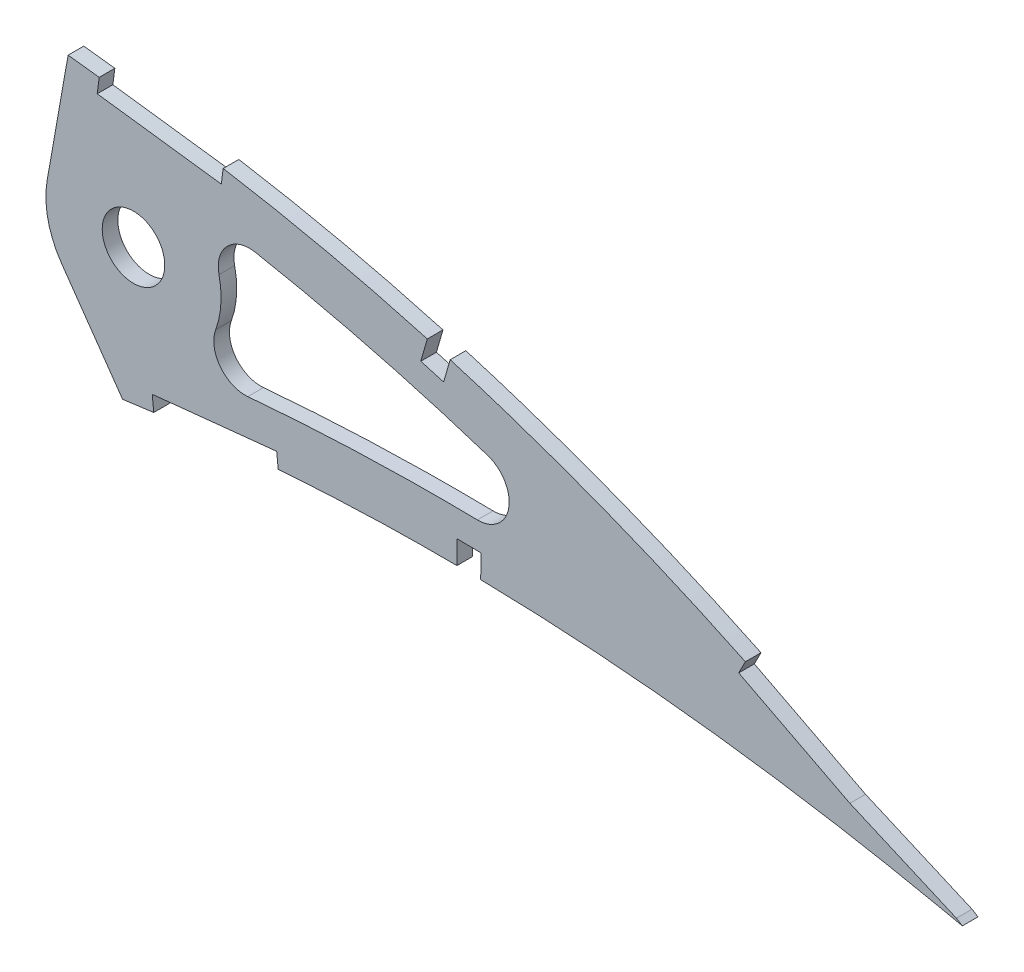
SolidWorks part; units mm, degrees
material "Plywood"
ref_plane "Front Plane" through (0, 0, 0) normal (0, 0, 1) x (1, 0, 0)
ref_plane "Top Plane" through (0, 0, 0) normal (0, 1, 0) x (1, 0, 0)
ref_plane "Right Plane" through (0, 0, 0) normal (1, 0, 0) x (0, 0, -1)
curve "Curve1"
  spline degree 3 poles (554.3197, 0.8642, 0) (554.2772, 0.8904, 0) (554.1075, 0.9953, 0) (553.7252, 1.2298, 0) (553.0885, 1.6204, 0) (552.1972, 2.1644, 0) (551.0519, 2.8603, 0) (549.6522, 3.7033, 0) (547.9988, 4.6906, 0) (546.0922, 5.8176, 0) (543.9326, 7.0789, 0) (541.5207, 8.4695, 0) (538.8569, 9.9815, 0) (535.942, 11.6087, 0) (532.7772, 13.3434, 0) (529.3631, 15.1777, 0) (525.7007, 17.1023, 0) (521.7917, 19.109, 0) (517.6366, 21.1866, 0) (513.2374, 23.3265, 0) (508.5956, 25.518, 0) (503.7128, 27.7495, 0) (498.5918, 30.0118, 0) (493.234, 32.2909, 0) (487.6424, 34.577, 0) (481.8195, 36.8569, 0) (475.7686, 39.1203, 0) (469.4922, 41.3526, 0) (462.9949, 43.5439, 0) (456.2798, 45.6802, 0) (449.3518, 47.7496, 0) (442.2149, 49.739, 0) (434.875, 51.6379, 0) (427.3368, 53.4327, 0) (419.6066, 55.1112, 0) (411.6907, 56.6635, 0) (403.5957, 58.0739, 0) (395.344, 59.3415, 0) (387.0683, 60.3958, 0) (378.8096, 61.4299, 0) (370.5633, 62.4014, 0) (362.2161, 63.3317, 0) (353.7762, 64.2156, 0) (345.252, 65.0503, 0) (336.6519, 65.8323, 0) (327.9851, 66.5592, 0) (319.2598, 67.227, 0) (310.4852, 67.8346, 0) (301.6702, 68.3766, 0) (292.8239, 68.8527, 0) (283.9555, 69.2595, 0) (275.0741, 69.5943, 0) (266.1892, 69.8549, 0) (257.3099, 70.039, 0) (248.446, 70.1454, 0) (239.6066, 70.171, 0) (230.8014, 70.1156, 0) (222.0395, 69.9772, 0) (213.3305, 69.7538, 0) (204.6838, 69.4452, 0) (196.1087, 69.0513, 0) (187.6145, 68.5689, 0) (179.2105, 68.0012, 0) (170.9059, 67.3456, 0) (162.7101, 66.6021, 0) (154.6315, 65.7736, 0) (146.6791, 64.8581, 0) (138.8614, 63.858, 0) (131.1871, 62.7754, 0) (123.6647, 61.6096, 0) (116.3022, 60.3641, 0) (109.1077, 59.04, 0) (102.0887, 57.6413, 0) (95.2529, 56.1683, 0) (88.6074, 54.6255, 0) (82.1593, 53.0155, 0) (75.9155, 51.3413, 0) (69.8822, 49.607, 0) (64.0656, 47.8163, 0) (58.4725, 45.9714, 0) (53.107, 44.0792, 0) (47.9758, 42.141, 0) (43.0829, 40.1629, 0) (38.4338, 38.1474, 0) (34.0322, 36.1008, 0) (29.883, 34.0255, 0) (25.9891, 31.9271, 0) (22.3545, 29.809, 0) (18.9827, 27.675, 0) (15.875, 25.5306, 0) (13.0358, 23.3771, 0) (10.4661, 21.22, 0) (8.1674, 19.0625, 0) (6.143, 16.9061, 0) (4.3929, 14.7547, 0) (2.9194, 12.6099, 0) (1.7228, 10.4738, 0) (0.8056, 8.3479, 0) (0.1671, 6.2334, 0) (-0.1824, 4.1334, 0) (-0.2694, 2.0463, 0) (-0.0897, 0.6811, 0) (0, 0, 0) knots 0 0 0 0 0.000254 0.001015 0.002283 0.004057 0.006331 0.009105 0.012374 0.016134 0.02038 0.025106 0.030306 0.035972 0.0421 0.048678 0.055702 0.06316 0.071046 0.07935 0.088063 0.097176 0.106678 0.116562 0.126814 0.137428 0.148394 0.1597 0.171338 0.183298 0.19557 0.208144 0.221012 0.234162 0.247587 0.261277 0.275223 0.289414 0.303771 0.317689 0.331784 0.34604 0.360444 0.374983 0.38964 0.404403 0.419257 0.434187 0.449177 0.464215 0.479284 0.49437 0.509458 0.524532 0.539579 0.554583 0.56953 0.584403 0.599191 0.613877 0.628447 0.642889 0.657186 0.671326 0.685294 0.699078 0.712665 0.726043 0.739198 0.752118 0.764792 0.777208 0.789356 0.801224 0.812804 0.824083 0.835055 0.84571 0.856038 0.866034 0.875689 0.884998 0.893953 0.902553 0.910789 0.918661 0.926166 0.933303 0.940071 0.946475 0.952518 0.958205 0.963547 0.968557 0.97325 0.977651 0.981787 0.985694 0.989415 0.993001 0.996508 1 1 1 1
curve "Curve2"
  spline degree 3 poles (0, 0, 0) (0.1423, -0.672, 0) (0.4277, -2.019, 0) (1.203, -3.9582, 0) (2.2282, -5.8223, 0) (3.5249, -7.6064, 0) (5.0845, -9.31, 0) (6.9036, -10.9348, 0) (8.9803, -12.4801, 0) (11.3119, -13.945, 0) (13.8951, -15.3312, 0) (16.7269, -16.6378, 0) (19.8048, -17.8643, 0) (23.1254, -19.0092, 0) (26.6846, -20.0741, 0) (30.4791, -21.0566, 0) (34.5045, -21.9578, 0) (38.7571, -22.7757, 0) (43.232, -23.5109, 0) (47.9248, -24.1631, 0) (52.8305, -24.7327, 0) (57.9444, -25.2185, 0) (63.2614, -25.6215, 0) (68.7762, -25.942, 0) (74.4834, -26.1811, 0) (80.3777, -26.3377, 0) (86.4531, -26.4144, 0) (92.7043, -26.4123, 0) (99.1251, -26.3308, 0) (105.71, -26.1745, 0) (112.4527, -25.9423, 0) (119.3471, -25.6371, 0) (126.387, -25.2619, 0) (133.5661, -24.818, 0) (140.8781, -24.3074, 0) (148.3166, -23.7341, 0) (155.8748, -23.0997, 0) (163.5462, -22.4077, 0) (171.324, -21.6617, 0) (179.2015, -20.864, 0) (187.1716, -20.0183, 0) (195.2274, -19.1275, 0) (203.3619, -18.1963, 0) (211.5677, -17.2262, 0) (219.8379, -16.223, 0) (228.1647, -15.1885, 0) (236.5412, -14.1266, 0) (244.9597, -13.0425, 0) (253.4125, -11.9359, 0) (261.8924, -10.8148, 0) (270.3912, -9.6781, 0) (278.9016, -8.5319, 0) (287.4156, -7.3796, 0) (295.925, -6.2216, 0) (304.4222, -5.0626, 0) (312.8995, -3.9059, 0) (321.3485, -2.7516, 0) (329.7616, -1.6054, 0) (338.1302, -0.4672, 0) (346.4467, 0.6607, 0) (354.7031, 1.775, 0) (362.8916, 2.8743, 0) (371.0037, 3.9578, 0) (379.0314, 5.0259, 0) (386.8463, 6.0463, 0) (394.4281, 7.0733, 0) (401.8022, 7.9152, 0) (409.0845, 8.6338, 0) (416.2825, 9.2229, 0) (423.3877, 9.6911, 0) (430.3918, 10.0417, 0) (437.2865, 10.2795, 0) (444.0631, 10.4116, 0) (450.7132, 10.4414, 0) (457.2276, 10.3785, 0) (463.598, 10.2277, 0) (469.8153, 9.9961, 0) (475.8709, 9.6912, 0) (481.7563, 9.3216, 0) (487.4626, 8.8925, 0) (492.9818, 8.4141, 0) (498.3055, 7.8933, 0) (503.4254, 7.336, 0) (508.334, 6.7541, 0) (513.0236, 6.1512, 0) (517.4871, 5.5374, 0) (521.7172, 4.9187, 0) (525.7074, 4.3032, 0) (529.4512, 3.6966, 0) (532.9427, 3.1071, 0) (536.1764, 2.5402, 0) (539.1467, 2.0013, 0) (541.8495, 1.4973, 0) (544.2794, 1.0307, 0) (546.4331, 0.6092, 0) (548.3068, 0.2346, 0) (549.8976, -0.0878, 0) (551.2027, -0.3567, 0) (552.2202, -0.5677, 0) (552.948, -0.7211, 0) (553.3854, -0.8124, 0) (553.5798, -0.8538, 0) (553.6283, -0.8642, 0) knots 0 0 0 0 0.003638 0.007293 0.011028 0.014901 0.018963 0.023258 0.027821 0.032679 0.037853 0.043362 0.049215 0.055422 0.061989 0.068918 0.076211 0.083868 0.091887 0.100266 0.109 0.118085 0.127515 0.137285 0.147388 0.157816 0.168563 0.179619 0.190977 0.202627 0.21456 0.226767 0.239236 0.251959 0.264924 0.27812 0.291536 0.30516 0.318981 0.332985 0.347163 0.361499 0.375981 0.390597 0.405333 0.420175 0.43511 0.450124 0.465203 0.480333 0.495501 0.51069 0.525887 0.541078 0.556247 0.571382 0.586466 0.601485 0.616424 0.631269 0.646007 0.660621 0.675098 0.689423 0.703582 0.716908 0.730009 0.742952 0.755726 0.76832 0.780724 0.792927 0.804916 0.816679 0.828204 0.839475 0.850481 0.861208 0.871639 0.881763 0.891564 0.901027 0.910139 0.918884 0.927249 0.935221 0.942785 0.949928 0.956638 0.962904 0.968712 0.974054 0.978918 0.983297 0.98718 0.990561 0.993433 0.995791 0.99763 0.998946 0.999737 1 1 1 1
sketch "Sketch1" plane through (0, 0, 0) normal (0, 0, 1) x (1, 0, 0)
  line L28 (0, 63.5) -> (-23.1981, 63.5) construction
  line L39 (379.9183, -27.3345) -> (379.9183, 27.3345) construction
  line L40 (368.4067, 59.4277) -> (353.2793, 2.9714) construction
  line L41 (537.5238, 0.838) -> (542.0214, -1.9404)
  line L42 (536.8534, -0.838) -> (542.0214, -1.9404)
  circle A0 centre (68.58, 6.35) radius 9.525 construction
  circle A1 centre (246.38, 6.35) radius 9.525 construction
  spline S3 degree 3 poles (0, 0) (0.138, -0.6516) (0.4147, -1.9578) (1.1665, -3.8383) (2.1607, -5.6459) (3.4181, -7.3759) (4.9305, -9.0279) (6.6944, -10.6035) (8.7082, -12.1019) (10.9692, -13.5225) (13.4741, -14.8667) (16.2201, -16.1336) (19.2047, -17.323) (22.4247, -18.4332) (25.8761, -19.4659) (29.5556, -20.4185) (33.4591, -21.2925) (37.5827, -22.0856) (41.9221, -22.7985) (46.4726, -23.431) (51.2297, -23.9833) (56.1887, -24.4544) (61.3446, -24.8452) (66.6923, -25.156) (72.2266, -25.3878) (77.9422, -25.5397) (83.8336, -25.6141) (89.8954, -25.612) (96.1216, -25.533) (102.507, -25.3814) (109.0454, -25.1563) (115.7309, -24.8603) (122.5575, -24.4965) (129.5191, -24.066) (136.6095, -23.5709) (143.8226, -23.015) (151.1518, -22.3997) (158.5908, -21.7287) (166.1329, -21.0053) (173.7717, -20.2318) (181.5003, -19.4118) (189.312, -18.5479) (197.2, -17.6449) (205.1572, -16.7043) (213.1768, -15.7315) (221.2513, -14.7283) (229.374, -13.6986) (237.5374, -12.6473) (245.7341, -11.5743) (253.957, -10.4871) (262.1983, -9.3849) (270.4508, -8.2734) (278.7069, -7.156) (286.9584, -6.033) (295.1983, -4.9092) (303.4187, -3.7876) (311.6117, -2.6683) (319.7698, -1.5568) (327.8848, -0.4531) (335.9493, 0.6407) (343.9556, 1.7212) (351.896, 2.7872) (359.7623, 3.8379) (367.5468, 4.8736) (375.1249, 5.8631) (382.4769, 6.859) (389.6276, 7.6754) (396.6892, 8.3722) (403.6691, 8.9435) (410.559, 9.3975) (417.3509, 9.7374) (424.0367, 9.968) (430.608, 10.0961) (437.0566, 10.1251) (443.3736, 10.064) (449.5509, 9.9178) (455.5799, 9.6932) (461.4521, 9.3976) (467.1591, 9.0391) (472.6925, 8.6231) (478.0445, 8.1591) (483.2068, 7.6541) (488.1716, 7.1138) (492.9315, 6.5494) (497.479, 5.9648) (501.8072, 5.3696) (505.9092, 4.7697) (509.7784, 4.1728) (513.4088, 3.5846) (516.7946, 3.013) (519.9303, 2.4632) (522.8106, 1.9407) (525.4315, 1.4519) (527.7877, 0.9995) (529.8762, 0.5907) (531.6931, 0.2275) (533.2357, -0.0851) (534.5012, -0.3459) (535.4879, -0.5505) (536.1937, -0.6992) (536.6178, -0.7878) (536.8063, -0.828) (536.8534, -0.838) knots 0 0 0 0 0.003638 0.007293 0.011028 0.014901 0.018963 0.023258 0.027821 0.032679 0.037853 0.043362 0.049215 0.055422 0.061989 0.068918 0.076211 0.083868 0.091887 0.100266 0.109 0.118085 0.127515 0.137285 0.147388 0.157816 0.168563 0.179619 0.190977 0.202627 0.21456 0.226767 0.239236 0.251959 0.264924 0.27812 0.291536 0.30516 0.318981 0.332985 0.347163 0.361499 0.375981 0.390597 0.405333 0.420175 0.43511 0.450124 0.465203 0.480333 0.495501 0.51069 0.525887 0.541078 0.556247 0.571382 0.586466 0.601485 0.616424 0.631269 0.646007 0.660621 0.675098 0.689423 0.703582 0.716908 0.730009 0.742952 0.755726 0.76832 0.780724 0.792927 0.804916 0.816679 0.828204 0.839475 0.850481 0.861208 0.871639 0.881763 0.891564 0.901027 0.910139 0.918884 0.927249 0.935221 0.942785 0.949928 0.956638 0.962904 0.968712 0.974054 0.978918 0.983297 0.98718 0.990561 0.993433 0.995791 0.99763 0.998946 0.999737 1 1 1 1
  spline S6 degree 3 poles (537.5238, 0.838) (537.4826, 0.8635) (537.3181, 0.9651) (536.9473, 1.1925) (536.3299, 1.5713) (535.4656, 2.0988) (534.3551, 2.7737) (532.9977, 3.5911) (531.3944, 4.5485) (529.5456, 5.6413) (527.4514, 6.8644) (525.1126, 8.2129) (522.5295, 9.6791) (519.703, 11.2569) (516.6341, 12.9391) (513.3234, 14.7178) (509.772, 16.5841) (505.9814, 18.53) (501.9522, 20.5446) (497.6863, 22.6197) (493.1852, 24.7448) (488.4503, 26.9087) (483.4845, 29.1025) (478.289, 31.3125) (472.8669, 33.5293) (467.2204, 35.7401) (461.3528, 37.9349) (455.2666, 40.0996) (448.9661, 42.2246) (442.4545, 44.296) (435.7364, 46.3028) (428.8157, 48.2319) (421.6983, 50.0733) (414.3885, 51.8137) (406.8926, 53.4414) (399.2165, 54.9466) (391.3668, 56.3143) (383.365, 57.5434) (375.3401, 58.5658) (367.3317, 59.5686) (359.3352, 60.5106) (351.241, 61.4127) (343.0568, 62.2698) (334.7908, 63.0793) (326.4514, 63.8376) (318.0471, 64.5425) (309.5862, 65.19) (301.0775, 65.7792) (292.5296, 66.3048) (283.9513, 66.7665) (275.3516, 67.161) (266.7393, 67.4856) (258.1236, 67.7383) (249.5134, 67.9168) (240.9181, 68.0199) (232.3465, 68.0449) (223.8081, 67.9911) (215.3117, 67.8569) (206.8666, 67.6403) (198.4819, 67.341) (190.1666, 66.959) (181.9298, 66.4913) (173.7804, 65.9407) (165.7275, 65.305) (157.78, 64.584) (149.9461, 63.7807) (142.2347, 62.8929) (134.6539, 61.9231) (127.2121, 60.8733) (119.9176, 59.7429) (112.7783, 58.535) (105.8017, 57.2511) (98.9954, 55.8947) (92.3667, 54.4664) (85.9226, 52.9703) (79.6699, 51.4091) (73.6153, 49.7857) (67.7648, 48.1039) (62.1244, 46.3675) (56.7008, 44.5785) (51.4979, 42.7436) (46.5222, 40.8641) (41.7775, 38.9459) (37.2693, 36.9916) (33.0011, 35.007) (28.9776, 32.9945) (25.2017, 30.9597) (21.6772, 28.9058) (18.4075, 26.8364) (15.394, 24.757) (12.6408, 22.6688) (10.1489, 20.577) (7.9199, 18.4849) (5.9569, 16.3939) (4.2598, 14.3076) (2.831, 12.2278) (1.6706, 10.1565) (0.7812, 8.095) (0.162, 6.0445) (-0.1769, 4.0082) (-0.2612, 1.9843) (-0.087, 0.6604) (0, 0) knots 0 0 0 0 0.000254 0.001015 0.002283 0.004057 0.006331 0.009105 0.012374 0.016134 0.02038 0.025106 0.030306 0.035972 0.0421 0.048678 0.055702 0.06316 0.071046 0.07935 0.088063 0.097176 0.106678 0.116562 0.126814 0.137428 0.148394 0.1597 0.171338 0.183298 0.19557 0.208144 0.221012 0.234162 0.247587 0.261277 0.275223 0.289414 0.303771 0.317689 0.331784 0.34604 0.360444 0.374983 0.38964 0.404403 0.419257 0.434187 0.449177 0.464215 0.479284 0.49437 0.509458 0.524532 0.539579 0.554583 0.56953 0.584403 0.599191 0.613877 0.628447 0.642889 0.657186 0.671326 0.685294 0.699078 0.712665 0.726043 0.739198 0.752118 0.764792 0.777208 0.789356 0.801224 0.812804 0.824083 0.835055 0.84571 0.856038 0.866034 0.875689 0.884998 0.893953 0.902553 0.910789 0.918661 0.926166 0.933303 0.940071 0.946475 0.952518 0.958205 0.963547 0.968557 0.97325 0.977651 0.981787 0.985694 0.989415 0.993001 0.996508 1 1 1 1
  point P10 (78.5929, 16.5948)
  point P11 (227.8303, 32.4941)
  dimension "D2" = 19.05
  dimension "D18" = 177.8
  dimension "D3" = 15
  dimension "D5" = 63.5
  dimension "D7" = 57.15
  dimension "D12" = 57.15
  dimension "D17" = 68.58
extrude "Boss-Extrude1" add sketch "Sketch1" along normal blind 3.175
sketch "Sketch4" plane through (0, 0, 0) normal (0, 0, -1) x (-1, 0, 0)
  line L0 (-356.287, 36.32) -> (-360.5267, 60.365)
  line L1 (-359.2323, 23.0344) -> (-371.5795, 5.4008)
  line L2 (-373.7968, 33.2326) -> (-412.6852, 33.2326)
  circle A0 centre (-373.7968, 33.2326) radius 17.78
  circle A1 centre (-373.7968, 33.2326) radius 6.35
  spline S0 degree 3 poles (-1632.0302, 1674.0962) (-565.4284, -22.6918) (-552.7247, -8.4851) (-536.9473, 1.1925) (-536.3299, 1.5713) (-535.4656, 2.0988) (-534.3551, 2.7737) (-532.9977, 3.5911) (-531.3944, 4.5485) (-529.5456, 5.6413) (-527.4514, 6.8644) (-525.1126, 8.2129) (-522.5295, 9.6791) (-519.703, 11.2569) (-516.6341, 12.9391) (-513.3234, 14.7178) (-509.772, 16.5841) (-505.9814, 18.53) (-501.9522, 20.5446) (-497.6863, 22.6197) (-493.1852, 24.7448) (-488.4503, 26.9087) (-483.4845, 29.1025) (-478.289, 31.3125) (-472.8669, 33.5293) (-467.2204, 35.7401) (-461.3528, 37.9349) (-455.2666, 40.0996) (-448.9661, 42.2246) (-442.4545, 44.296) (-435.7364, 46.3028) (-428.8157, 48.2319) (-421.6983, 50.0733) (-414.3885, 51.8137) (-406.8926, 53.4414) (-399.2165, 54.9466) (-391.3668, 56.3143) (-383.365, 57.5434) (-375.3401, 58.5658) (-367.3317, 59.5686) (-359.3352, 60.5106) (-351.241, 61.4127) (-343.0568, 62.2698) (-334.7908, 63.0793) (-326.4514, 63.8376) (-318.0471, 64.5425) (-309.5862, 65.19) (-301.0775, 65.7792) (-292.5296, 66.3048) (-283.9513, 66.7665) (-275.3516, 67.161) (-266.7393, 67.4856) (-258.1236, 67.7383) (-249.5134, 67.9168) (-240.9181, 68.0199) (-232.3465, 68.0449) (-223.8081, 67.9911) (-215.3117, 67.8569) (-206.8666, 67.6403) (-198.4819, 67.341) (-190.1666, 66.959) (-181.9298, 66.4913) (-173.7804, 65.9407) (-165.7275, 65.305) (-157.78, 64.584) (-149.9461, 63.7807) (-142.2347, 62.8929) (-134.6539, 61.9231) (-127.2121, 60.8733) (-119.9176, 59.7429) (-112.7783, 58.535) (-105.8017, 57.2511) (-98.9954, 55.8947) (-92.3667, 54.4664) (-85.9226, 52.9703) (-79.6699, 51.4091) (-73.6153, 49.7857) (-67.7648, 48.1039) (-62.1244, 46.3675) (-56.7008, 44.5785) (-51.4979, 42.7436) (-46.5222, 40.8641) (-41.7775, 38.9459) (-37.2693, 36.9916) (-33.0011, 35.007) (-28.9776, 32.9945) (-25.2017, 30.9597) (-21.6772, 28.9058) (-18.4075, 26.8364) (-15.394, 24.757) (-12.6408, 22.6688) (-10.1489, 20.577) (-7.9199, 18.4849) (-5.9569, 16.3939) (-4.2598, 14.3076) (-2.831, 12.2278) (-1.6706, 10.1565) (-0.7812, 8.095) (-0.162, 6.0445) (0.1769, 4.0082) (1.1707, -19.8347) (-66.7598, -38.6935) (1990.434, -189.4699) knots -0.094882 -0.094882 -0.094882 -0.094882 0.000254 0.001015 0.002283 0.004057 0.006331 0.009105 0.012374 0.016134 0.02038 0.025106 0.030306 0.035972 0.0421 0.048678 0.055702 0.06316 0.071046 0.07935 0.088063 0.097176 0.106678 0.116562 0.126814 0.137428 0.148394 0.1597 0.171338 0.183298 0.19557 0.208144 0.221012 0.234162 0.247587 0.261277 0.275223 0.289414 0.303771 0.317689 0.331784 0.34604 0.360444 0.374983 0.38964 0.404403 0.419257 0.434187 0.449177 0.464215 0.479284 0.49437 0.509458 0.524532 0.539579 0.554583 0.56953 0.584403 0.599191 0.613877 0.628447 0.642889 0.657186 0.671326 0.685294 0.699078 0.712665 0.726043 0.739198 0.752118 0.764792 0.777208 0.789356 0.801224 0.812804 0.824083 0.835055 0.84571 0.856038 0.866034 0.875689 0.884998 0.893953 0.902553 0.910789 0.918661 0.926166 0.933303 0.940071 0.946475 0.952518 0.958205 0.963547 0.968557 0.97325 0.977651 0.981787 0.985694 0.989415 0.993001 0.996508 1.114113 1.114113 1.114113 1.114113 only from (-537.5238, 0.838) to (0, 0) construction
  spline S1 degree 3 poles (1940.1203, -483.4322) (-49.9299, 58.7424) (7.7069, 18.357) (-1.1665, -3.8383) (-2.1607, -5.6459) (-3.4181, -7.3759) (-4.9305, -9.0279) (-6.6944, -10.6035) (-8.7082, -12.1019) (-10.9692, -13.5225) (-13.4741, -14.8667) (-16.2201, -16.1336) (-19.2047, -17.323) (-22.4247, -18.4332) (-25.8761, -19.4659) (-29.5556, -20.4185) (-33.4591, -21.2925) (-37.5827, -22.0856) (-41.9221, -22.7985) (-46.4726, -23.431) (-51.2297, -23.9833) (-56.1887, -24.4544) (-61.3446, -24.8452) (-66.6923, -25.156) (-72.2266, -25.3878) (-77.9422, -25.5397) (-83.8336, -25.6141) (-89.8954, -25.612) (-96.1216, -25.533) (-102.507, -25.3814) (-109.0454, -25.1563) (-115.7309, -24.8603) (-122.5575, -24.4965) (-129.5191, -24.066) (-136.6095, -23.5709) (-143.8226, -23.015) (-151.1518, -22.3997) (-158.5908, -21.7287) (-166.1329, -21.0053) (-173.7717, -20.2318) (-181.5003, -19.4118) (-189.312, -18.5479) (-197.2, -17.6449) (-205.1572, -16.7043) (-213.1768, -15.7315) (-221.2513, -14.7283) (-229.374, -13.6986) (-237.5374, -12.6473) (-245.7341, -11.5743) (-253.957, -10.4871) (-262.1983, -9.3849) (-270.4508, -8.2734) (-278.7069, -7.156) (-286.9584, -6.033) (-295.1983, -4.9092) (-303.4187, -3.7876) (-311.6117, -2.6683) (-319.7698, -1.5568) (-327.8848, -0.4531) (-335.9493, 0.6407) (-343.9556, 1.7212) (-351.896, 2.7872) (-359.7623, 3.8379) (-367.5468, 4.8736) (-375.1249, 5.8631) (-382.4769, 6.859) (-389.6276, 7.6754) (-396.6892, 8.3722) (-403.6691, 8.9435) (-410.559, 9.3975) (-417.3509, 9.7374) (-424.0367, 9.968) (-430.608, 10.0961) (-437.0566, 10.1251) (-443.3736, 10.064) (-449.5509, 9.9178) (-455.5799, 9.6932) (-461.4521, 9.3976) (-467.1591, 9.0391) (-472.6925, 8.6231) (-478.0445, 8.1591) (-483.2068, 7.6541) (-488.1716, 7.1138) (-492.9315, 6.5494) (-497.479, 5.9648) (-501.8072, 5.3696) (-505.9092, 4.7697) (-509.7784, 4.1728) (-513.4088, 3.5846) (-516.7946, 3.013) (-519.9303, 2.4632) (-522.8106, 1.9407) (-525.4315, 1.4519) (-527.7877, 0.9995) (-529.8762, 0.5907) (-531.6931, 0.2275) (-533.2357, -0.0851) (-534.5012, -0.3459) (-535.4879, -0.5505) (-536.1937, -0.6992) (-552.4366, -4.0895) (-567.1821, -13.3973) (-997.8539, 1944.6618) knots -0.119141 -0.119141 -0.119141 -0.119141 0.003638 0.007293 0.011028 0.014901 0.018963 0.023258 0.027821 0.032679 0.037853 0.043362 0.049215 0.055422 0.061989 0.068918 0.076211 0.083868 0.091887 0.100266 0.109 0.118085 0.127515 0.137285 0.147388 0.157816 0.168563 0.179619 0.190977 0.202627 0.21456 0.226767 0.239236 0.251959 0.264924 0.27812 0.291536 0.30516 0.318981 0.332985 0.347163 0.361499 0.375981 0.390597 0.405333 0.420175 0.43511 0.450124 0.465203 0.480333 0.495501 0.51069 0.525887 0.541078 0.556247 0.571382 0.586466 0.601485 0.616424 0.631269 0.646007 0.660621 0.675098 0.689423 0.703582 0.716908 0.730009 0.742952 0.755726 0.76832 0.780724 0.792927 0.804916 0.816679 0.828204 0.839475 0.850481 0.861208 0.871639 0.881763 0.891564 0.901027 0.910139 0.918884 0.927249 0.935221 0.942785 0.949928 0.956638 0.962904 0.968712 0.974054 0.978918 0.983297 0.98718 0.990561 0.993433 0.995791 0.99763 0.998946 0.999737 1.088404 1.088404 1.088404 1.088404 only from (0, 0) to (-536.8534, -0.838) construction
  spline S2 degree 3 poles (-537.5238, 0.838) (-537.4826, 0.8635) (-537.3181, 0.9651) (-536.9473, 1.1925) (-536.3299, 1.5713) (-535.4656, 2.0988) (-534.3551, 2.7737) (-532.9977, 3.5911) (-531.3944, 4.5485) (-529.5456, 5.6413) (-527.4514, 6.8644) (-525.1126, 8.2129) (-522.5295, 9.6791) (-519.703, 11.2569) (-516.6341, 12.9391) (-513.3234, 14.7178) (-509.772, 16.5841) (-505.9814, 18.53) (-501.9522, 20.5446) (-497.6863, 22.6197) (-493.1852, 24.7448) (-488.4503, 26.9087) (-483.4845, 29.1025) (-478.289, 31.3125) (-472.8669, 33.5293) (-467.2204, 35.7401) (-461.3528, 37.9349) (-455.2666, 40.0996) (-448.9661, 42.2246) (-442.4545, 44.296) (-435.7364, 46.3028) (-428.8157, 48.2319) (-421.6983, 50.0733) (-414.3885, 51.8137) (-406.8926, 53.4414) (-399.2165, 54.9466) (-391.3668, 56.3143) (-383.365, 57.5434) (-375.3401, 58.5658) (-367.3317, 59.5686) (-359.3352, 60.5106) (-351.241, 61.4127) (-343.0568, 62.2698) (-334.7908, 63.0793) (-326.4514, 63.8376) (-318.0471, 64.5425) (-309.5862, 65.19) (-301.0775, 65.7792) (-292.5296, 66.3048) (-283.9513, 66.7665) (-275.3516, 67.161) (-266.7393, 67.4856) (-258.1236, 67.7383) (-249.5134, 67.9168) (-240.9181, 68.0199) (-232.3465, 68.0449) (-223.8081, 67.9911) (-215.3117, 67.8569) (-206.8666, 67.6403) (-198.4819, 67.341) (-190.1666, 66.959) (-181.9298, 66.4913) (-173.7804, 65.9407) (-165.7275, 65.305) (-157.78, 64.584) (-149.9461, 63.7807) (-142.2347, 62.8929) (-134.6539, 61.9231) (-127.2121, 60.8733) (-119.9176, 59.7429) (-112.7783, 58.535) (-105.8017, 57.2511) (-98.9954, 55.8947) (-92.3667, 54.4664) (-85.9226, 52.9703) (-79.6699, 51.4091) (-73.6153, 49.7857) (-67.7648, 48.1039) (-62.1244, 46.3675) (-56.7008, 44.5785) (-51.4979, 42.7436) (-46.5222, 40.8641) (-41.7775, 38.9459) (-37.2693, 36.9916) (-33.0011, 35.007) (-28.9776, 32.9945) (-25.2017, 30.9597) (-21.6772, 28.9058) (-18.4075, 26.8364) (-15.394, 24.757) (-12.6408, 22.6688) (-10.1489, 20.577) (-7.9199, 18.4849) (-5.9569, 16.3939) (-4.2598, 14.3076) (-2.831, 12.2278) (-1.6706, 10.1565) (-0.7812, 8.095) (-0.162, 6.0445) (0.1769, 4.0082) (0.2612, 1.9843) (0.087, 0.6604) (0, 0) knots 0 0 0 0 0.000254 0.001015 0.002283 0.004057 0.006331 0.009105 0.012374 0.016134 0.02038 0.025106 0.030306 0.035972 0.0421 0.048678 0.055702 0.06316 0.071046 0.07935 0.088063 0.097176 0.106678 0.116562 0.126814 0.137428 0.148394 0.1597 0.171338 0.183298 0.19557 0.208144 0.221012 0.234162 0.247587 0.261277 0.275223 0.289414 0.303771 0.317689 0.331784 0.34604 0.360444 0.374983 0.38964 0.404403 0.419257 0.434187 0.449177 0.464215 0.479284 0.49437 0.509458 0.524532 0.539579 0.554583 0.56953 0.584403 0.599191 0.613877 0.628447 0.642889 0.657186 0.671326 0.685294 0.699078 0.712665 0.726043 0.739198 0.752118 0.764792 0.777208 0.789356 0.801224 0.812804 0.824083 0.835055 0.84571 0.856038 0.866034 0.875689 0.884998 0.893953 0.902553 0.910789 0.918661 0.926166 0.933303 0.940071 0.946475 0.952518 0.958205 0.963547 0.968557 0.97325 0.977651 0.981787 0.985694 0.989415 0.993001 0.996508 1 1 1 1
  spline S3 degree 3 poles (0, 0) (-0.138, -0.6516) (-0.4147, -1.9578) (-1.1665, -3.8383) (-2.1607, -5.6459) (-3.4181, -7.3759) (-4.9305, -9.0279) (-6.6944, -10.6035) (-8.7082, -12.1019) (-10.9692, -13.5225) (-13.4741, -14.8667) (-16.2201, -16.1336) (-19.2047, -17.323) (-22.4247, -18.4332) (-25.8761, -19.4659) (-29.5556, -20.4185) (-33.4591, -21.2925) (-37.5827, -22.0856) (-41.9221, -22.7985) (-46.4726, -23.431) (-51.2297, -23.9833) (-56.1887, -24.4544) (-61.3446, -24.8452) (-66.6923, -25.156) (-72.2266, -25.3878) (-77.9422, -25.5397) (-83.8336, -25.6141) (-89.8954, -25.612) (-96.1216, -25.533) (-102.507, -25.3814) (-109.0454, -25.1563) (-115.7309, -24.8603) (-122.5575, -24.4965) (-129.5191, -24.066) (-136.6095, -23.5709) (-143.8226, -23.015) (-151.1518, -22.3997) (-158.5908, -21.7287) (-166.1329, -21.0053) (-173.7717, -20.2318) (-181.5003, -19.4118) (-189.312, -18.5479) (-197.2, -17.6449) (-205.1572, -16.7043) (-213.1768, -15.7315) (-221.2513, -14.7283) (-229.374, -13.6986) (-237.5374, -12.6473) (-245.7341, -11.5743) (-253.957, -10.4871) (-262.1983, -9.3849) (-270.4508, -8.2734) (-278.7069, -7.156) (-286.9584, -6.033) (-295.1983, -4.9092) (-303.4187, -3.7876) (-311.6117, -2.6683) (-319.7698, -1.5568) (-327.8848, -0.4531) (-335.9493, 0.6407) (-343.9556, 1.7212) (-351.896, 2.7872) (-359.7623, 3.8379) (-367.5468, 4.8736) (-375.1249, 5.8631) (-382.4769, 6.859) (-389.6276, 7.6754) (-396.6892, 8.3722) (-403.6691, 8.9435) (-410.559, 9.3975) (-417.3509, 9.7374) (-424.0367, 9.968) (-430.608, 10.0961) (-437.0566, 10.1251) (-443.3736, 10.064) (-449.5509, 9.9178) (-455.5799, 9.6932) (-461.4521, 9.3976) (-467.1591, 9.0391) (-472.6925, 8.6231) (-478.0445, 8.1591) (-483.2068, 7.6541) (-488.1716, 7.1138) (-492.9315, 6.5494) (-497.479, 5.9648) (-501.8072, 5.3696) (-505.9092, 4.7697) (-509.7784, 4.1728) (-513.4088, 3.5846) (-516.7946, 3.013) (-519.9303, 2.4632) (-522.8106, 1.9407) (-525.4315, 1.4519) (-527.7877, 0.9995) (-529.8762, 0.5907) (-531.6931, 0.2275) (-533.2357, -0.0851) (-534.5012, -0.3459) (-535.4879, -0.5505) (-536.1937, -0.6992) (-536.6178, -0.7878) (-536.8063, -0.828) (-536.8534, -0.838) knots 0 0 0 0 0.003638 0.007293 0.011028 0.014901 0.018963 0.023258 0.027821 0.032679 0.037853 0.043362 0.049215 0.055422 0.061989 0.068918 0.076211 0.083868 0.091887 0.100266 0.109 0.118085 0.127515 0.137285 0.147388 0.157816 0.168563 0.179619 0.190977 0.202627 0.21456 0.226767 0.239236 0.251959 0.264924 0.27812 0.291536 0.30516 0.318981 0.332985 0.347163 0.361499 0.375981 0.390597 0.405333 0.420175 0.43511 0.450124 0.465203 0.480333 0.495501 0.51069 0.525887 0.541078 0.556247 0.571382 0.586466 0.601485 0.616424 0.631269 0.646007 0.660621 0.675098 0.689423 0.703582 0.716908 0.730009 0.742952 0.755726 0.76832 0.780724 0.792927 0.804916 0.816679 0.828204 0.839475 0.850481 0.861208 0.871639 0.881763 0.891564 0.901027 0.910139 0.918884 0.927249 0.935221 0.942785 0.949928 0.956638 0.962904 0.968712 0.974054 0.978918 0.983297 0.98718 0.990561 0.993433 0.995791 0.99763 0.998946 0.999737 1 1 1 1
  spline S4 degree 1 poles (-532.1841, -7.8057) (-10.0219, 1.7185) knots 0 0 1 1 construction
  spline S5 degree 1 poles (-10.0219, 1.7185) (-538.9729, 9.0984) knots 0 0 1 1 construction
  spline S6 degree 3 poles (-532.1841, -7.8057) (-532.035, -7.7136) (-531.7436, -7.5345) (-531.1023, -7.1412) (-530.0303, -6.4862) (-527.85, -5.1645) (-523.4829, -2.5651) (-514.6678, 2.5066) (-496.7411, 12.095) (-470.3238, 24.1396) (-442.9694, 33.791) (-420.6386, 39.9785) (-406.5149, 43.1961) (-395.1531, 45.3637) (-386.5599, 46.8051) (-378.0384, 47.9972) (-369.1749, 49.1011) (-360.4166, 50.162) (-348.6799, 51.484) (-328.147, 53.5808) (-298.749, 55.9238) (-263.4315, 57.6196) (-228.1119, 58.0844) (-192.8506, 57.171) (-157.7356, 54.6709) (-128.7085, 51.0365) (-105.7459, 46.987) (-88.7097, 43.306) (-71.9299, 38.8842) (-58.261, 34.4734) (-47.6305, 30.4115) (-39.8596, 27.063) (-32.3674, 23.3733) (-25.2794, 19.2928) (-18.8179, 14.7781) (-14.319, 10.6534) (-11.7187, 7.3378) (-10.6606, 5.4268) (-10.2382, 4.2645) (-10.0884, 3.6968) (-10.0101, 3.295) (-9.9553, 2.8496) (-9.9432, 2.5723) (-9.9453, 2.4518) (-9.9493, 2.3713) (-9.9688, 2.1598) (-9.9949, 1.9339) (-10.0132, 1.7875) (-10.0219, 1.7185) knots 0 0 0 0 0.000976 0.001952 0.003903 0.007807 0.015613 0.031226 0.062452 0.124904 0.187357 0.218583 0.249809 0.265422 0.281035 0.296648 0.312261 0.327874 0.343487 0.374713 0.437166 0.499618 0.56207 0.624522 0.686974 0.749427 0.780653 0.811879 0.843105 0.874331 0.889944 0.905557 0.92117 0.936783 0.952396 0.968009 0.975816 0.983623 0.987526 0.989477 0.991429 0.993381 0.995332 0.996308 0.997284 0.99826 0.998748 0.999236 0.999236 0.999236 0.999236
  spline S7 degree 3 poles (-10.0219, 1.7185) (-10.0361, 1.6529) (-10.0665, 1.5144) (-10.1157, 1.2979) (-10.1669, 1.0931) (-10.1938, 1.0009) (-10.2267, 0.9008) (-10.3197, 0.6625) (-10.5705, 0.1458) (-10.9157, -0.4199) (-11.7404, -1.469) (-13.2635, -2.8937) (-16.5705, -5.1355) (-21.8641, -7.6046) (-29.0738, -9.8943) (-36.7462, -11.652) (-44.6834, -12.9788) (-52.7844, -13.9626) (-63.7273, -14.8945) (-77.583, -15.4719) (-94.3476, -15.4772) (-111.1866, -14.9569) (-133.6938, -13.7131) (-161.8825, -11.3422) (-195.7357, -7.6685) (-229.6092, -3.472) (-263.4966, 1.0208) (-297.4142, 5.6457) (-325.6956, 9.51) (-345.5133, 12.184) (-356.8358, 13.6973) (-363.916, 14.6412) (-369.594, 15.387) (-373.812, 15.9419) (-378.0525, 16.5127) (-382.4211, 17.0728) (-386.7861, 17.5755) (-392.5828, 18.1876) (-402.7738, 19.115) (-417.3468, 20.0031) (-440.7096, 20.5101) (-469.8877, 19.4483) (-498.8731, 16.2543) (-518.9745, 12.9996) (-528.9918, 11.1265) (-533.6061, 10.2081) (-535.7587, 9.7686) (-536.8071, 9.5524) (-537.7352, 9.359) (-538.3978, 9.2197) (-538.786, 9.1383) (-538.9729, 9.0984) knots 0.000796 0.000796 0.000796 0.000796 0.001284 0.001772 0.002748 0.003724 0.004699 0.006651 0.008603 0.012506 0.016409 0.024215 0.032021 0.047634 0.063247 0.078859 0.094472 0.110084 0.125697 0.156922 0.188147 0.219372 0.250597 0.313047 0.375498 0.437948 0.500398 0.562848 0.625299 0.656524 0.672136 0.687749 0.695555 0.703361 0.711168 0.718974 0.72678 0.734587 0.750199 0.781424 0.812649 0.8751 0.93755 0.968775 0.984387 0.992194 0.994145 0.996097 0.998048 0.999024 1 1 1 1
  dimension "D1" = 35.56
  dimension "D3" = 80
  dimension "D4" = 55
  dimension "D2" = 10.16
extrude "Cut-Extrude2" cut sketch "Sketch4" against normal through all
sketch "Sketch5" plane through (0, 0, 3.175) normal (0, 0, 1) x (1, 0, 0)
  line L1 (392.0264, 56.3907) -> (366.8423, 59.6743)
  line L3 (391.616, 53.2426) -> (392.0264, 56.3907)
  line L5 (402.8557, 11.8924) -> (377.5967, 9.2826)
  line L7 (438.0805, 45.6488) -> (433.4452, 46.9876)
  line L9 (436.7417, 41.0136) -> (438.0805, 45.6488)
  line L11 (403.1819, 8.735) -> (402.8557, 11.8924)
  line L13 (444.3268, 14.772) -> (439.5023, 14.8365)
  line L15 (444.2624, 9.9476) -> (444.3268, 14.772)
  line L17 (520.5603, 11.064) -> (498.0773, 22.6526)
  line L19 (543.7622, 0.9878) -> (520.5603, 11.064)
  line L21 (377.9229, 6.1253) -> (403.1819, 8.735)
  line L23 (366.4319, 56.5263) -> (391.616, 53.2426)
  line L25 (439.4379, 10.012) -> (444.2624, 9.9476)
  line L27 (432.1064, 42.3524) -> (436.7417, 41.0136)
  line L29 (496.6227, 19.8304) -> (519.1997, 8.1935)
  line L31 (519.1997, 8.1935) -> (542.4974, -1.9245)
  line L33 (542.4974, -1.9245) -> (543.7622, 0.9878)
  line L35 (433.4452, 46.9876) -> (432.1064, 42.3524)
  line L37 (498.0773, 22.6526) -> (496.6227, 19.8304)
  line L39 (439.5023, 14.8365) -> (439.4379, 10.012)
  line L41 (377.5967, 9.2826) -> (377.9229, 6.1253)
  line L43 (366.8423, 59.6743) -> (366.4319, 56.5263)
extrude "Cut-Extrude3" cut sketch "Sketch5" against normal blind 7.62
fillet "Fillet1" radius 6.35 3 edges at (483.9453, 17.7821, 1.5875) (380.7081, 16.8508, 1.5875) (385.0563, 46.9931, 1.5875)
move or copy body "Body-Move/Copy1" [suppressed] bodies to move or copy 127 parameters "D1"=0, "D2"=0, "D3"=0
